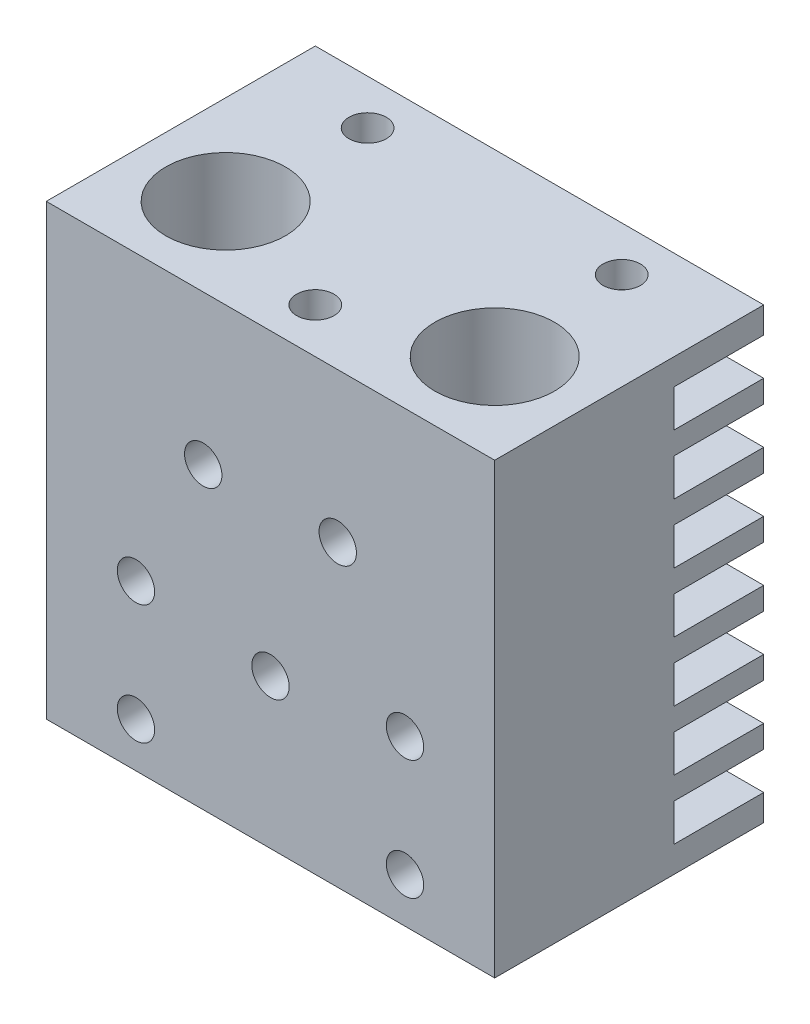
SolidWorks part; units mm, degrees
material "6061-T6 (SS)"
ref_plane "Front Plane" through (0, 0, 0) normal (0, 0, 1) x (1, 0, 0)
ref_plane "Top Plane" through (0, 0, 0) normal (0, 1, 0) x (1, 0, 0)
ref_plane "Right Plane" through (0, 0, 0) normal (1, 0, 0) x (0, 0, -1)
sketch "Sketch1" plane through (0, 0, 0) normal (0, 1, 0) x (1, 0, 0)
  line L1 (15, 9) -> (-15, 9)
  line L2 (15, 9) -> (15, -9)
  line L3 (15, -9) -> (-15, -9)
  line L4 (-15, 9) -> (-15, -9)
  line L5 (15, 9) -> (-15, -9) construction
  line L6 (15, -9) -> (-15, 9) construction
  point P0 (0, 0)
  dimension "D1" = 18
  dimension "D2" = 30
extrude "Boss-Extrude1" add sketch "Sketch1" along normal blind 30
sketch "Sketch2" plane through (0, 30, 0) normal (0, 1, 0) x (1, 0, 0)
  line L0 (-15, 6) -> (15, 6) construction
  line L1 (-15, 9) -> (-15, -9) construction
  line L2 (15, -9) -> (15, 9) construction
  line L3 (-15, -9) -> (15, -9) construction
  line L4 (-15, -6) -> (15, -6) construction
  line L5 (-15, -3) -> (15, -3) construction
  circle A0 centre (0, -6) radius 1.25
  circle A1 centre (-8.5, 6) radius 1.25
  circle A2 centre (8.5, 6) radius 1.25
  dimension "D3" = 2.5
  dimension "D4" = 23.5
  dimension "D5" = 6.5
  dimension "D6" = 2.5
  dimension "D7" = 2.5
  dimension "D1" = 15
  dimension "D2" = 3
  dimension "D8" = 6
extrude "Cut-Extrude1" cut sketch "Sketch2" against normal blind 8
sketch "Sketch3" plane through (0, 30, 0) normal (0, 1, 0) x (1, 0, 0)
  line L0 (-9, -3) -> (9, -3) construction
  line L1 (-15, -9) -> (15, -9) construction
  line L2 (15, -9) -> (15, 9) construction
  circle A0 centre (-9, -3) radius 4
  circle A1 centre (9, -3) radius 4
  dimension "D2" = 8
  dimension "D3" = 8
  dimension "D1" = 6
  dimension "D4" = 6
  dimension "D5" = 18
extrude "Cut-Extrude2" cut sketch "Sketch3" against normal blind 6.5
sketch "Sketch4" plane through (0, 23.5, 0) normal (0, 1, 0) x (1, 0, 0)
  circle A0 centre (9, -3) radius 2.1
  circle A1 centre (-9, -3) radius 2.1
  dimension "D1" = 4.2
  dimension "D2" = 4.2
extrude "Cut-Extrude3" cut sketch "Sketch4" against normal through all
sketch "Sketch5" plane through (15, 0, 0) normal (1, 0, 0) x (0, 0, -1)
  line L0 (9, 30) -> (9, 0) construction
  line L1 (3, 8.25) -> (15, 8.25)
  line L2 (15, 8.25) -> (15, 5.75)
  line L3 (3, 5.75) -> (15, 5.75)
  line L4 (3, 8.25) -> (3, 5.75)
  line L5 (3, 12.25) -> (15, 12.25)
  line L6 (15, 12.25) -> (15, 9.75)
  line L7 (-9, 0) -> (9, 0) construction
  line L8 (3, 9.75) -> (15, 9.75)
  line L9 (3, 12.25) -> (3, 9.75)
  line L10 (3, 16.25) -> (15, 16.25)
  line L11 (15, 16.25) -> (15, 13.75)
  line L12 (3, 13.75) -> (15, 13.75)
  line L13 (3, 16.25) -> (3, 13.75)
  line L14 (3, 20.25) -> (15, 20.25)
  line L15 (15, 20.25) -> (15, 17.75)
  line L16 (3, 17.75) -> (15, 17.75)
  line L17 (3, 20.25) -> (3, 17.75)
  line L18 (3, 24.25) -> (15, 24.25)
  line L19 (15, 24.25) -> (15, 21.75)
  line L20 (3, 21.75) -> (15, 21.75)
  line L21 (3, 24.25) -> (3, 21.75)
  line L22 (3, 28.25) -> (15, 28.25)
  line L23 (15, 28.25) -> (15, 25.75)
  line L24 (3, 25.75) -> (15, 25.75)
  line L25 (3, 28.25) -> (3, 25.75)
  line L26 (-9, 30) -> (9, 30) construction
  line L38 (3, 4.25) -> (15, 4.25)
  line L39 (3, 4.25) -> (3, 1.75)
  line L40 (3, 1.75) -> (15, 1.75)
  line L41 (15, 4.25) -> (15, 1.75)
  line L42 (3, 4.25) -> (15, 1.75) construction
  line L43 (3, 1.75) -> (15, 4.25) construction
  point P32 (9, 3)
  dimension "D1" = 2.5
  dimension "D2" = 1.75
  dimension "D3" = 6
  dimension "D5" = 1.75
  dimension "D4" = 7
extrude "Cut-Extrude4" cut sketch "Sketch5" against normal up to next
sketch "Sketch6" plane through (0, 0, 0) normal (0, -1, 0) x (1, 0, 0)
  circle A0 centre (9, 3) radius 3.45
  circle A1 centre (-9, 3) radius 3.45
  dimension "D1" = 6.9
  dimension "D2" = 6.9
extrude "Cut-Extrude5" cut sketch "Sketch6" against normal blind 14
sketch "Sketch7" plane through (0, 0, 9) normal (0, 0, 1) x (1, 0, 0)
  line L0 (9, 30) -> (9, 0) construction
  line L1 (-15, 30) -> (15, 30) construction
  line L2 (-15, 0) -> (15, 0) construction
  line L3 (15, 30) -> (15, 0) construction
  line L4 (-9, 30) -> (-9, 0) construction
  line L5 (-15, 3) -> (15, 3) construction
  line L6 (-15, 30) -> (-15, 0) construction
  line L7 (15, 11) -> (-15, 11) construction
  line L8 (0, 0) -> (0, 30) construction
  line L9 (-15, 20) -> (15, 20) construction
  circle A0 centre (-4.5, 20) radius 1.25
  circle A1 centre (4.5, 20) radius 1.25
  circle A2 centre (-9, 11) radius 1.25
  circle A3 centre (-9, 3) radius 1.25
  circle A4 centre (9, 11) radius 1.25
  circle A5 centre (9, 3) radius 1.25
  circle A6 centre (0, 10) radius 1.25
  dimension "D1" = 2.5
  dimension "D2" = 2.5
  dimension "D3" = 2.5
  dimension "D4" = 2.5
  dimension "D5" = 2.5
  dimension "D6" = 2.5
  dimension "D7" = 2.5
  dimension "D15" = 19.5
  dimension "D8" = 6
  dimension "D9" = 18
  dimension "D10" = 3
  dimension "D11" = 11
  dimension "D12" = 10
  dimension "D13" = 20
  dimension "D14" = 10.5
extrude "Cut-Extrude6" cut sketch "Sketch7" against normal through all
chamfer "Chamfer1" distance 1.7 angle 21 2 edges at (-9, 23.5, 5.1) (9, 23.5, 5.1)
